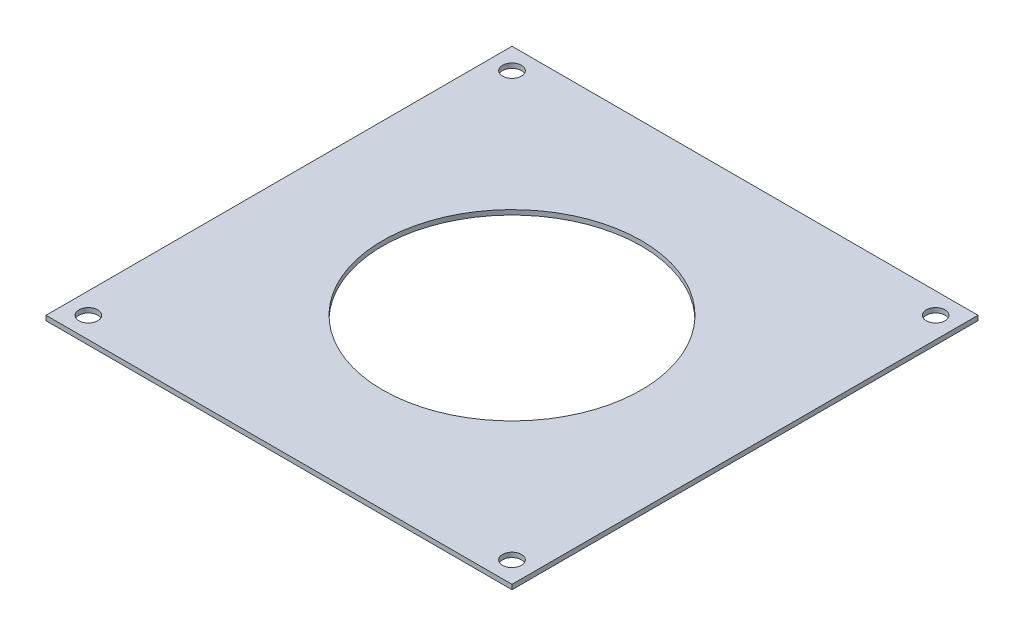
SolidWorks part; units mm, degrees
material "1023 Carbon Steel Sheet (SS)"
ref_plane "Front Plane" through (0, 0, 0) normal (0, 0, 1) x (1, 0, 0)
ref_plane "Top Plane" through (0, 0, 0) normal (0, 1, 0) x (1, 0, 0)
ref_plane "Right Plane" through (0, 0, 0) normal (1, 0, 0) x (0, 0, -1)
sketch "Sketch1" plane through (0, 0, 0) normal (0, 1, 0) x (1, 0, 0)
  line L1 (-49.3914, -49.3914) -> (49.3914, -49.3914)
  line L2 (-49.3914, -49.3914) -> (-49.3914, 49.3914)
  line L3 (-49.3914, 49.3914) -> (49.3914, 49.3914)
  line L4 (49.3914, -49.3914) -> (49.3914, 49.3914)
  line L5 (-49.3914, -49.3914) -> (49.3914, 49.3914) construction
  line L6 (-49.3914, 49.3914) -> (49.3914, -49.3914) construction
  point P0 (0, 0)
  dimension "D1" = 139.7
extrude "Boss-Extrude1" add sketch "Sketch1" along normal blind 1
sketch "Sketch3" plane through (0, 0, 0) normal (0, 1, 0) x (1, 0, 0)
  line L0 (-49.3914, -49.3914) -> (49.3914, 49.3914) construction
  line L1 (-44.9013, 44.9013) -> (44.9013, -44.9013) construction
  circle A0 centre (44.9013, 44.9013) radius 2
  circle A1 centre (44.9013, -44.9013) radius 2
  circle A2 centre (-44.9013, -44.9013) radius 2
  circle A3 centre (-44.9013, 44.9013) radius 2
  point P15 (0, 0)
  dimension "D3" = 4
  dimension "D2" = 127
  dimension "D1" = 4
extrude "Cut-Extrude2" cut sketch "Sketch3" along normal through all
sketch "Sketch4" plane through (0, 0, 0) normal (0, 1, 0) x (1, 0, 0)
  circle A0 centre (0, 0) radius 27.432 construction
  circle A1 centre (0, 0) radius 27.432
extrude "Cut-Extrude3" cut sketch "Sketch4" along normal through all
equation "\"D1@Boss-Extrude1\"=1mm"
equation "\"D3@Sketch3\"=4mm"
